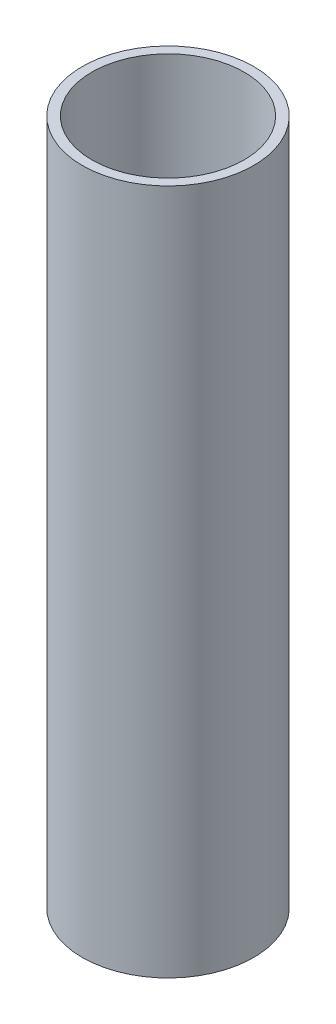
SolidWorks part; units mm, degrees
ref_plane "Front Plane" through (0, 0, 0) normal (0, 0, 1) x (1, 0, 0)
ref_plane "Top Plane" through (0, 0, 0) normal (0, 1, 0) x (1, 0, 0)
ref_plane "Right Plane" through (0, 0, 0) normal (1, 0, 0) x (0, 0, -1)
sketch "Sketch1" plane through (0, 0, 0) normal (0, 1, 0) x (1, 0, 0)
  circle A0 centre (0, 0) radius 6.35
  circle A1 centre (0, 0) radius 5.6388
  dimension "D1" = 12.7
  dimension "D2" = 11.2776
extrude "Boss-Extrude1" add sketch "Sketch1" along normal blind 50.8
